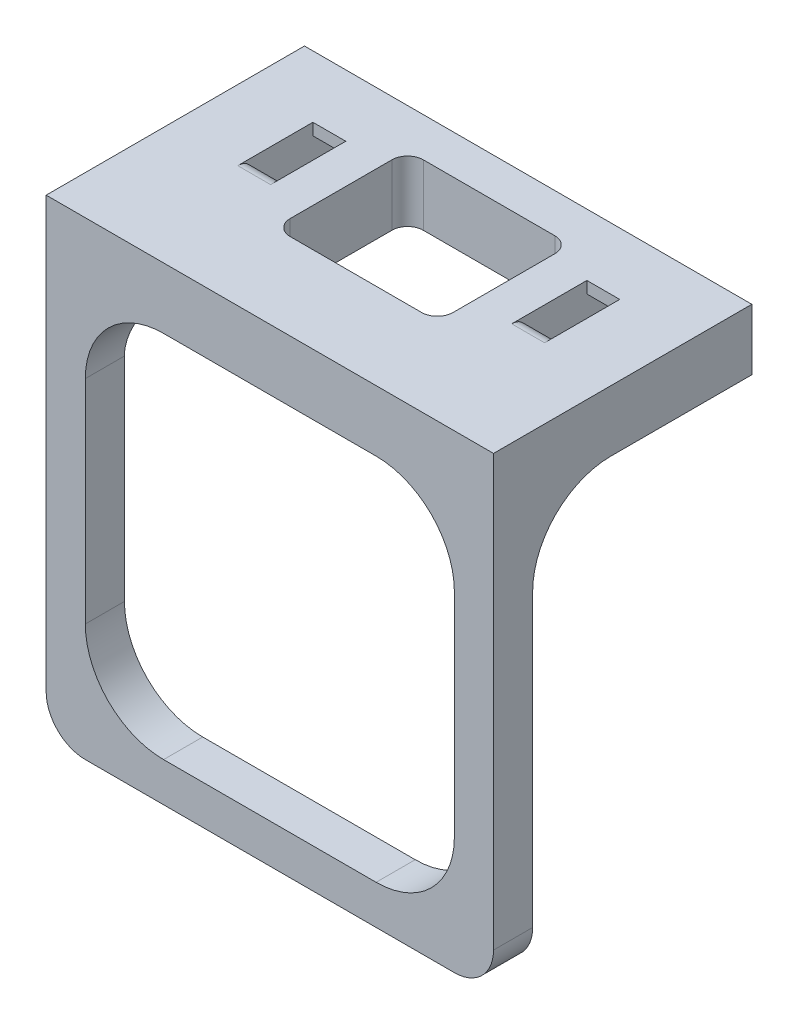
SolidWorks part; units mm, degrees
ref_plane "Front Plane" through (0, 0, 0) normal (0, 0, 1) x (1, 0, 0)
ref_plane "Top Plane" through (0, 0, 0) normal (0, 1, 0) x (1, 0, 0)
ref_plane "Right Plane" through (0, 0, 0) normal (1, 0, 0) x (0, 0, -1)
sketch "Sketch1" plane through (0, 0, 0) normal (0, 1, 0) x (1, 0, 0)
  line L1 (0, 33) -> (57.15, 33)
  line L2 (0, 33) -> (0, 0)
  line L3 (0, 0) -> (57.15, 0)
  line L4 (57.15, 33) -> (57.15, 0)
  dimension "D1" = 0
  dimension "D2" = 0
  dimension "D3" = 33
  dimension "D4" = 57.15
extrude "Boss-Extrude1" add sketch "Sketch1" along normal blind 10
sketch "Sketch2" plane through (0, 10, 0) normal (0, 1, 0) x (1, 0, 0)
  line L0 (28.575, 33) -> (28.575, 9.4174)
  line L1 (8.975, 28.5) -> (13.175, 28.5)
  line L2 (8.975, 28.5) -> (8.975, 17.5)
  line L3 (8.975, 17.5) -> (13.175, 17.5)
  line L4 (13.175, 28.5) -> (13.175, 17.5)
  line L5 (57.15, 33) -> (0, 33) construction
  line L6 (0, 0) -> (57.15, 0) construction
  line L7 (48.175, 17.5) -> (43.975, 17.5)
  line L8 (43.975, 28.5) -> (43.975, 17.5)
  line L9 (48.175, 28.5) -> (43.975, 28.5)
  line L10 (48.175, 28.5) -> (48.175, 17.5)
  dimension "D1" = 4.2
  dimension "D2" = 15.4
  dimension "D3" = 17.5
  dimension "D4" = 11
extrude "Cut-Extrude1" cut sketch "Sketch2" against normal blind 5.8 contours L4 L1 L2 L3 | L10 L9 L8 L7
sketch "Sketch3" plane through (13.175, 0, 0) normal (-1, 0, 0) x (0, 0, 1)
  line L0 (-28.5, 5.85) -> (-25.1, 8.5)
  line L1 (-28.5, 4.2) -> (-28.5, 10) construction
  line L2 (-25.1, 8.5) -> (-25.1, 10)
  line L3 (-28.5, 10) -> (-17.5, 10) construction
  line L4 (-28.5, 4.2) -> (-17.5, 4.2) construction
  line L5 (-28.5, 5.85) -> (-28.5, 10)
  line L6 (-28.5, 10) -> (-25.1, 10)
  dimension "D1" = 1.65
  dimension "D2" = 3.4
  dimension "D3" = 1.5
extrude "Boss-Extrude2" add sketch "Sketch3" along normal blind 55.8 from surface at -43.975 starting at face at (57.15, 5, -16.5)
sketch "Sketch4" plane through (57.15, 0, 0) normal (1, 0, 0) x (0, 0, -1)
  line L0 (33, 10) -> (33, 0) construction
  line L1 (0, 0) -> (33, 0)
  line L2 (0, 0) -> (0, 2.2)
  line L3 (0, 2.2) -> (33, 2.2)
  line L4 (33, 0) -> (33, 2.2)
  line L5 (28.5, 4.2) -> (17.5, 4.2) construction
  dimension "D1" = 2
extrude "Cut-Extrude2" cut sketch "Sketch4" against normal through all both and the other way through all
fillet "Fillet1" radius 2 2 edges at (46.075, 10, -17.5) (11.075, 10, -17.5)
sketch "Sketch5" plane through (0, 10, 0) normal (0, 1, 0) x (1, 0, 0)
  line L0 (57.15, 0) -> (57.15, 33) construction
  line L1 (0, 0) -> (57.15, 0)
  line L2 (0, 0) -> (0, 5)
  line L3 (0, 5) -> (57.15, 5)
  line L4 (57.15, 0) -> (57.15, 5)
  dimension "D1" = 5
sketch "Sketch7" plane through (0, 10, 0) normal (0, 1, 0) x (1, 0, 0)
  line L0 (13.175, 25.1) -> (13.175, 15.5) construction
  line L1 (18.175, 28) -> (38.975, 28)
  line L2 (18.175, 28) -> (18.175, 11)
  line L3 (18.175, 11) -> (38.975, 11)
  line L4 (38.975, 28) -> (38.975, 11)
  line L5 (43.975, 25.1) -> (43.975, 15.5) construction
  line L6 (57.15, 33) -> (0, 33) construction
  line L8 (0, 0) -> (57.15, 0) construction
  dimension "D1" = 5
  dimension "D2" = 5
  dimension "D3" = 5
  dimension "D4" = 11
extrude "Cut-Extrude4" cut sketch "Sketch7" against normal blind 16
fillet "Fillet2" radius 2 4 edges at (38.975, 6.1, -11) (18.175, 6.1, -11) (18.175, 6.1, -28) (38.975, 6.1, -28)
extrude "Boss-Extrude4" add sketch "Sketch5" against normal blind 52.15 from surface at -7.8 starting at face at (28.575, 2.2, -19.5)
sketch "Sketch8" plane through (0, 0, -5) normal (0, 0, -1) x (-1, 0, 0)
  line L0 (0, 10) -> (0, -49.95) construction
  line L1 (-52.15, -44.95) -> (-5, -44.95)
  line L2 (-52.15, -44.95) -> (-52.15, 2.2)
  line L3 (-52.15, 2.2) -> (-5, 2.2)
  line L4 (-5, -44.95) -> (-5, 2.2)
  line L5 (0, -49.95) -> (-57.15, -49.95) construction
  line L6 (-57.15, 10) -> (-57.15, -49.95) construction
  line L7 (-57.15, 2.2) -> (0, 2.2) construction
  dimension "D1" = 5
  dimension "D2" = 5
  dimension "D3" = 5
  dimension "D4" = 0
extrude "Cut-Extrude5" cut sketch "Sketch8" against normal blind 52.15
fillet "Fillet3" radius 10 6 edges at (5, -44.95, -2.5) (52.15, -44.95, -2.5) (54.65, 2.2, -5) (52.15, 2.2, -2.5) (2.5, 2.2, -5) (5, 2.2, -2.5)
fillet "Fillet4" radius 5 2 edges at (0, -49.95, -2.5) (57.15, -49.95, -2.5)
sketch "Sketch9" plane through (0, 0, 0) normal (0, 0, 1) x (1, 0, 0)
  line L3 (5, -34.95) -> (5, -7.8) construction
  line L4 (42.15, -44.95) -> (15, -44.95) construction
  circle A0 centre (28.575, -21.375) radius 20
  point P6 (0, 0)
  dimension "D3" = 40
  dimension "D1" = 23.575
  dimension "D2" = 23.575
sketch "Sketch10" plane through (0, 0, 0) normal (0, 0, 1) x (1, 0, 0)
  line L0 (5, -21.375) -> (52.15, -21.375)
  line L1 (5, -34.95) -> (5, -7.8) construction
  line L2 (52.15, -7.8) -> (52.15, -34.95) construction
